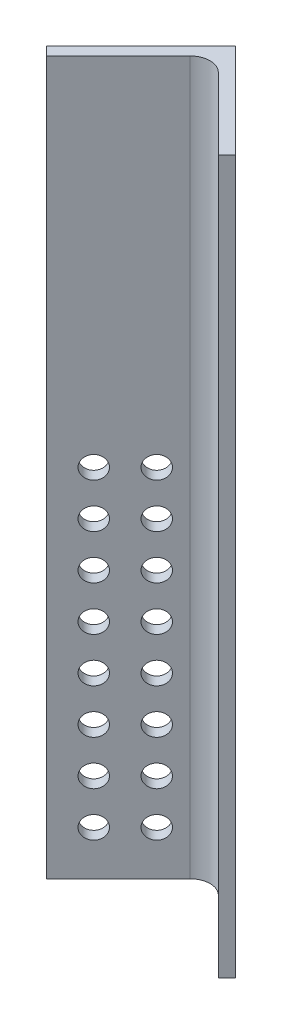
SolidWorks part; units mm, degrees
ref_plane "Front Plane" through (0, 0, 0) normal (0, 0, 1) x (1, 0, 0)
ref_plane "Top Plane" through (0, 0, 0) normal (0, 1, 0) x (1, 0, 0)
ref_plane "Right Plane" through (0, 0, 0) normal (1, 0, 0) x (0, 0, -1)
sketch "Sketch1" plane through (0, 0, 0) normal (0, 1, 0) x (1, 0, 0)
  line L0 (0, 0) -> (-26.9408, -26.9408)
  line L1 (-26.9408, -26.9408) -> (-24.4981, -29.3834)
  line L2 (-24.4981, -29.3834) -> (0, -4.8853)
  line L3 (0, -4.8853) -> (24.4981, -29.3834)
  line L4 (24.4981, -29.3834) -> (26.9408, -26.9408)
  line L5 (26.9408, -26.9408) -> (0, 0)
  line L6 (0, 0) -> (0, -4.8853) construction
  dimension "D1" = 38.1
  dimension "D2" = 38.1
  dimension "D3" = 3.4544
extrude "Boss-Extrude1" add sketch "Sketch1" along normal mid plane 203.2
fillet "Fillet1" radius 5.715 1 edges at (0, 0, 4.8853)
hole_wizard "1/4 (0.25) Diameter Hole1" positions "Sketch4" profile "Sketch3" hole size "1/4" standard "ANSI Inch" end condition up to next
sketch "Sketch4" plane through (2.4426, 0, 2.4426) normal (0.7071, 0, 0.7071) x (0.7071, 0, -0.7071)
  line L0 (-38.1, 101.6) -> (-38.1, -101.6) construction
  line L1 (-38.1, -101.6) -> (-9.1694, -101.6) construction
  point P0 (-28.575, 0)
  dimension "D1" = 9.525
  dimension "D2" = 101.6
sketch "Sketch3" plane through (-17.7629, 0, 22.6482) normal (0, 1, 0) x (0.7071, 0, -0.7071)
  line L0 (0, 0) -> (0, 3.4544)
  line L1 (0, 3.4544) -> (3.175, 3.4544)
  line L2 (3.175, 3.4544) -> (3.175, 0)
  line L5 (3.175, 0) -> (0, 0)
  line L11 (0, -6.35) -> (0, 107.95) construction
  dimension "Thru Hole Dia." = 6.35
  dimension "Thru Hole Depth" = 3.4544
pattern_linear "LPattern1" count 2 spacing 12.7 along (0.7071, 0, -0.7071) count 8 spacing 12.7 along (0, -1, 0) of "1/4 (0.25) Diameter Hole1"
